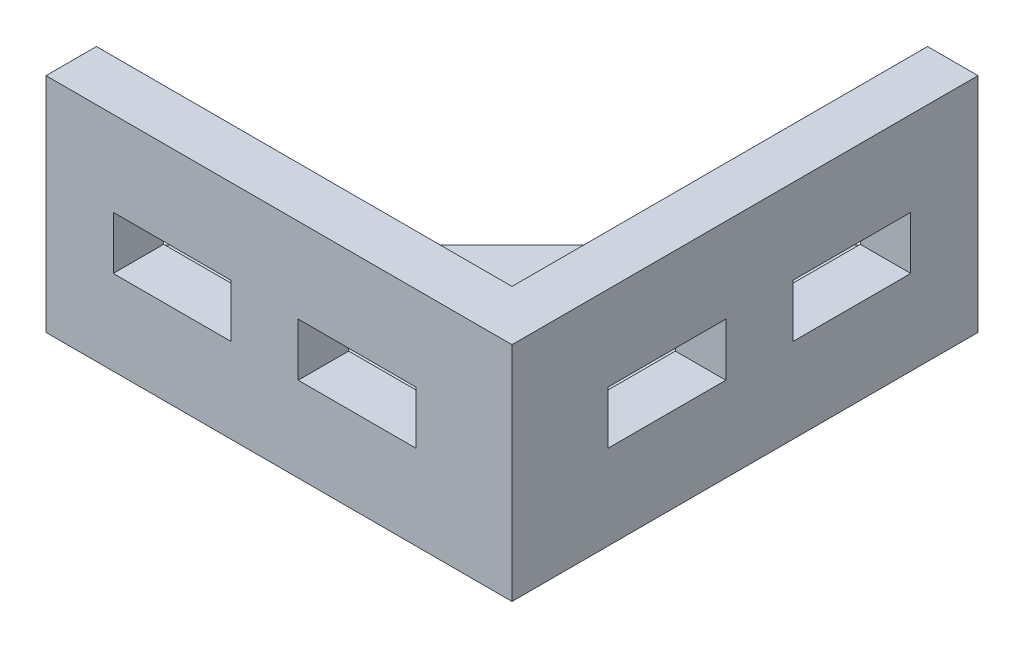
SolidWorks part; units mm, degrees
ref_plane "Front Plane" through (0, 0, 0) normal (0, 0, 1) x (1, 0, 0)
ref_plane "Top Plane" through (0, 0, 0) normal (0, 1, 0) x (1, 0, 0)
ref_plane "Right Plane" through (0, 0, 0) normal (1, 0, 0) x (0, 0, -1)
sketch "Sketch1" plane through (0, 0, 0) normal (0, 1, 0) x (1, 0, 0)
  line L0 (0, 0) -> (-88, 0)
  line L1 (-88, 0) -> (-88, 9.525)
  line L2 (-88, 9.525) -> (-9.525, 9.525)
  line L3 (-9.525, 9.525) -> (-9.525, 88)
  line L4 (-9.525, 88) -> (0, 88)
  line L5 (0, 88) -> (0, 0)
  point P8 (-0.4992, 0.7362)
  dimension "D1" = 88
  dimension "D2" = 88
  dimension "D3" = 9.525
  dimension "D4" = 9.525
extrude "Boss-Extrude1" add sketch "Sketch1" along normal blind 42
sketch "Sketch2" plane through (0, 0, 0) normal (0, 1, 0) x (1, 0, 0)
  line L0 (-9.525, 88) -> (-88, 9.525)
  line L1 (-88, 9.525) -> (-9.525, 9.525)
  line L2 (-9.525, 9.525) -> (-9.525, 88)
extrude "Boss-Extrude2" add sketch "Sketch2" along normal blind 9.525
sketch "Sketch3" plane through (0, 0, -9.525) normal (0, 0, -1) x (-1, 0, 0)
  line L0 (18.15, 26) -> (18.15, 16)
  line L1 (18.15, 16) -> (40.375, 16)
  line L2 (40.375, 16) -> (40.375, 26)
  line L3 (40.375, 26) -> (18.15, 26)
  line L4 (46.2718, 0) -> (46.2718, 42) construction
  line L5 (53.075, 26) -> (75.3, 26)
  line L6 (53.075, 26) -> (53.075, 16)
  line L7 (53.075, 16) -> (75.3, 16)
  line L8 (75.3, 26) -> (75.3, 16)
  line L9 (9.525, 0) -> (88, 0) construction
  line L10 (9.525, 42) -> (88, 42) construction
  line L11 (46.2718, 21) -> (40.375, 21) construction
  line L12 (88, 42) -> (88, 9.525) construction
  dimension "D1" = 10
  dimension "D2" = 22.225
  dimension "D3" = 22.225
  dimension "D4" = 12.7
  dimension "D5" = 12.7
extrude "Cut-Extrude1" cut sketch "Sketch3" against normal blind 9.525
sketch "Sketch4" plane through (-9.525, 0, 0) normal (-1, 0, 0) x (0, 0, 1)
  line L0 (-39.9503, 0) -> (-39.9503, 42) construction
  line L1 (-18.15, 16) -> (-40.375, 16)
  line L2 (-18.15, 16) -> (-18.15, 26)
  line L3 (-18.15, 26) -> (-40.375, 26)
  line L4 (-40.375, 16) -> (-40.375, 26)
  line L5 (-53.075, 16) -> (-75.3, 16)
  line L6 (-53.075, 16) -> (-53.075, 26)
  line L7 (-53.075, 26) -> (-75.3, 26)
  line L8 (-75.3, 16) -> (-75.3, 26)
  line L9 (-88, 0) -> (-9.525, 0) construction
  line L10 (-88, 42) -> (-9.525, 42) construction
  line L12 (-39.9503, 21) -> (-53.075, 21) construction
  line L13 (-88, 42) -> (-88, 9.525) construction
  dimension "D1" = 10
  dimension "D2" = 22.225
  dimension "D3" = 22.225
  dimension "D4" = 12.7
  dimension "D5" = 12.7
extrude "Cut-Extrude2" cut sketch "Sketch4" against normal blind 9.525
equation "\"D3@Sketch3\"=\"D2@Sketch3\""
equation "\"D3@Sketch4\"=\"D2@Sketch4\""
